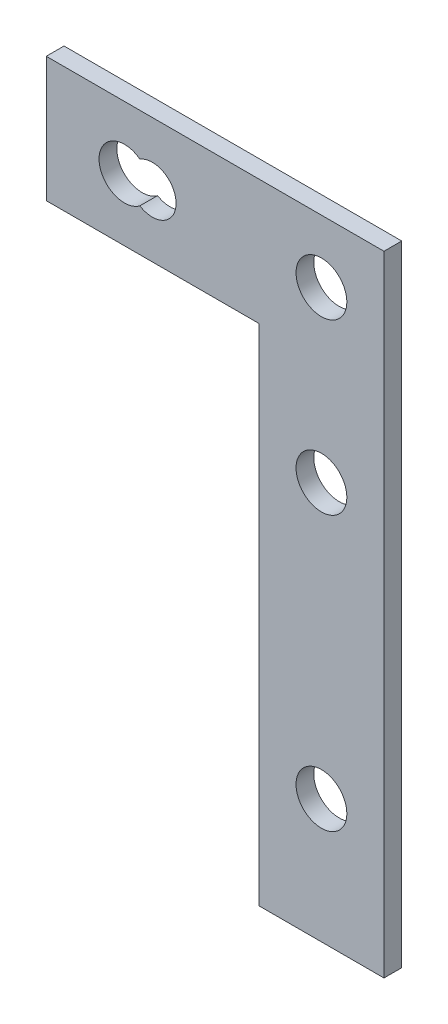
SolidWorks part; units mm, degrees
ref_plane "Front Plane" through (0, 0, 0) normal (0, 0, 1) x (1, 0, 0)
ref_plane "Top Plane" through (0, 0, 0) normal (0, 1, 0) x (1, 0, 0)
ref_plane "Right Plane" through (0, 0, 0) normal (1, 0, 0) x (0, 0, -1)
sketch "Sketch1" plane through (0, 0, 0) normal (0, 0, 1) x (1, 0, 0)
  line L0 (19.2532, 19.2532) -> (-19.2532, 19.2532)
  line L1 (31.9532, -31.9532) -> (19.2532, -31.9532)
  line L2 (31.9532, -31.9532) -> (31.9532, 31.9532)
  line L3 (31.9532, 31.9532) -> (-31.9532, 31.9532)
  line L4 (-19.2532, 19.2532) -> (-31.9532, 19.2532)
  line L5 (-31.9532, 19.2532) -> (-31.9532, 31.9532)
  line L7 (19.2532, -19.2532) -> (19.2532, -31.9532)
  line L9 (19.2532, -19.2532) -> (19.2532, 19.2532)
  line L10 (-19.2532, 19.2532) -> (19.2532, 19.2532)
  line L11 (-31.9532, -31.9532) -> (-31.9532, 31.9532) construction
  line L14 (31.9532, -31.9532) -> (-31.9532, -31.9532) construction
  line L16 (-19.2532, -19.2532) -> (-19.2532, 19.2532) construction
  line L18 (19.2532, -19.2532) -> (-19.2532, -19.2532) construction
  point P0 (0, 0)
extrude "Boss-Extrude2" add sketch "Sketch1" against normal blind 1.8034 contours L9 L7 L1 L2 L3 L5 L4 L0
hole_wizard "#97 (0.0059) Diameter Hole1" positions "Sketch3" profile "Sketch2" hole size "#97" standard "ANSI Inch" end condition through all
sketch "Sketch3" plane through (0, 0, 0) normal (0, 0, 1) x (1, 0, 0)
  line L3 (-31.9532, 19.2532) -> (-31.9532, 31.9532) construction
  line L4 (31.9532, -31.9532) -> (19.2532, -31.9532) construction
  point P0 (-19.3802, 25.6032)
  point P2 (8.4328, 25.6032)
  point P4 (25.6032, -19.3802)
  point P6 (25.6032, 8.4328)
  point P16 (-31.9532, 25.6032)
  dimension "D1" = 12.573
  dimension "D2" = 12.573
  dimension "D3" = 27.813
  dimension "D4" = 27.813
sketch "Sketch2" plane through (-19.3802, 25.6032, 0) normal (1, 0, 0) x (0, -1, 0)
  line L0 (0, 0) -> (0, 1.8034)
  line L1 (0, 1.8034) -> (2.413, 1.8034)
  line L2 (2.413, 1.8034) -> (2.413, 0)
  line L5 (2.413, 0) -> (0, 0)
  line L11 (0, -6.35) -> (0, 107.95) construction
  dimension "Thru Hole Dia." = 4.826
  dimension "Thru Hole Depth" = 1.8034
sketch "Sketch4" plane through (0, 0, 0) normal (0, 0, 1) x (1, 0, 0)
  circle A0 centre (5.6032, 25.6032) radius 2.1157 construction
hole_wizard "13/64 (0.20313) Diameter Hole1" positions "Sketch6" profile "Sketch5" hole size "13/64" standard "ANSI Inch" end condition through all
sketch "Sketch6" plane through (0, 0, 0) normal (0, 0, 1) x (1, 0, 0)
  point P0 (5.6032, 25.6032)
  point P4 (25.6032, 8.4328)
  point P7 (25.6032, -19.3802)
  point P11 (25.6032, 25.6032)
sketch "Sketch5" plane through (5.6032, 25.6032, 0) normal (1, 0, 0) x (0, -1, 0)
  line L0 (0, 0) -> (0, 1.8034)
  line L1 (0, 1.8034) -> (2.5798, 1.8034)
  line L2 (2.5798, 1.8034) -> (2.5798, 0)
  line L5 (2.5798, 0) -> (0, 0)
  line L11 (0, -6.35) -> (0, 107.95) construction
  dimension "Thru Hole Dia." = 5.1595
  dimension "Thru Hole Depth" = 1.8034
sketch "Sketch7" plane through (0, 0, 0) normal (0, 0, 1) x (1, 0, 0)
  line L1 (31.9532, 31.9532) -> (-31.9532, 31.9532) construction
  line L2 (-2.3368, 31.9532) -> (-2.3368, 19.2532)
  line L3 (19.2532, 19.2532) -> (-31.9532, 19.2532) construction
  line L4 (-2.3368, 19.2532) -> (-31.9532, 19.2532)
  line L5 (-31.9532, 19.2532) -> (-31.9532, 31.9532)
  line L6 (-31.9532, 19.2532) -> (-31.9532, 31.9532) construction
  line L7 (-31.9532, 31.9532) -> (-2.3368, 31.9532)
extrude "Cut-Extrude1" cut sketch "Sketch7" against normal blind 2.54
